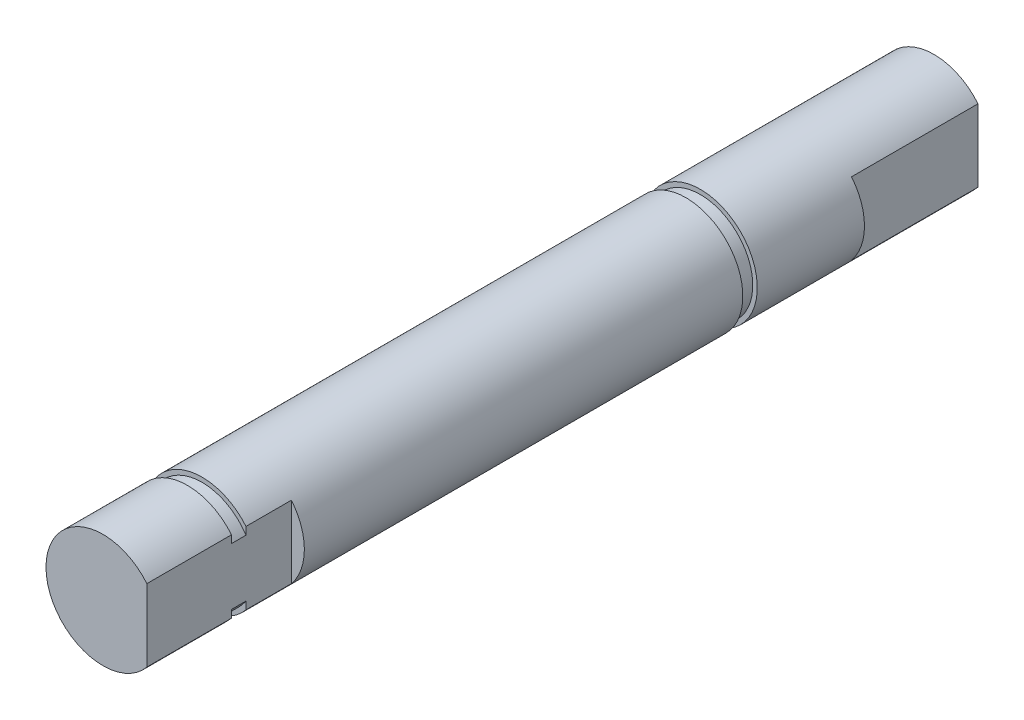
SolidWorks part; units mm, degrees
ref_plane "Front Plane" through (0, 0, 0) normal (0, 0, 1) x (1, 0, 0)
ref_plane "Top Plane" through (0, 0, 0) normal (0, 1, 0) x (1, 0, 0)
ref_plane "Right Plane" through (0, 0, 0) normal (1, 0, 0) x (0, 0, -1)
sketch "Sketch1" plane through (0, 0, 0) normal (0, 0, 1) x (1, 0, 0)
  circle A0 centre (0, 0) radius 4
  dimension "D1" = 8
extrude "Boss-Extrude1" add sketch "Sketch1" along normal blind 58.42
sketch "Sketch2" plane through (0, 0, 58.42) normal (0, 0, 1) x (1, 0, 0)
  line L0 (3.09, 2.54) -> (3.09, -2.54)
  circle A0 centre (0, 0) radius 4 construction
  arc A1 (3.09, -2.54) -> (3.09, 2.54) centre (0, 0) ccw
  dimension "D1" = 5.08
extrude "Cut-Extrude1" cut sketch "Sketch2" against normal blind 10.16
sketch "Sketch6" plane through (0, 0, 0) normal (0, 0, -1) x (-1, 0, 0)
  line L0 (-3.09, 2.54) -> (-3.09, -2.54) construction
  line L1 (-3.09, 2.54) -> (-3.09, -2.54)
  circle A2 centre (0, 0) radius 4 construction
  arc A3 (-3.09, 2.54) -> (-3.09, -2.54) centre (0, 0) ccw
extrude "Cut-Extrude5" cut sketch "Sketch6" against normal blind 8.89
sketch "Sketch4" plane through (0, 0, 0) normal (0, 0, -1) x (-1, 0, 0)
  circle A0 centre (0, 0) radius 3.683
  circle A1 centre (0, 0) radius 4 construction
  dimension "D1" = 7.366
extrude "Cut-Extrude3" cut sketch "Sketch4" against normal blind 1.016 from offset 16.4234 flip side to cut offset against normal yes
sketch "Sketch5" plane through (0, 0, 58.42) normal (0, 0, 1) x (1, 0, 0)
  circle A0 centre (0, 0) radius 3.683
  arc A1 (3.09, 2.54) -> (3.09, -2.54) centre (0, 0) ccw construction
  dimension "D1" = 7.366
extrude "Cut-Extrude4" cut sketch "Sketch5" against normal blind 1.016 from offset 5.95 flip side to cut
